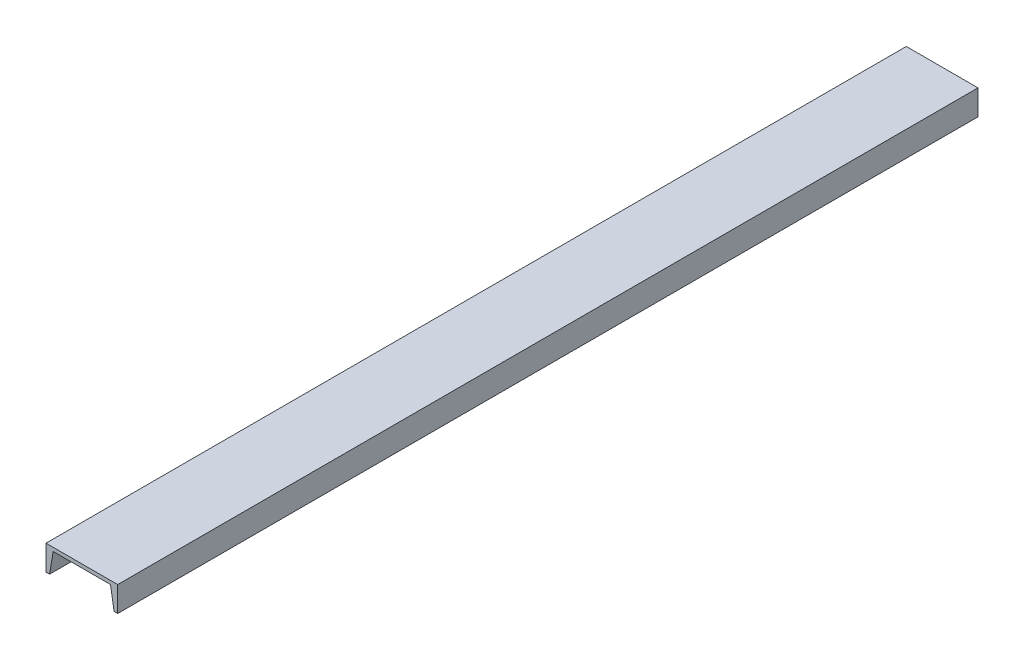
SolidWorks part; units mm, degrees
material "ASTM A36 Steel"
ref_plane "Front Plane" through (0, 0, 0) normal (0, 0, 1) x (1, 0, 0)
ref_plane "Top Plane" through (0, 0, 0) normal (0, 1, 0) x (1, 0, 0)
ref_plane "Right Plane" through (0, 0, 0) normal (1, 0, 0) x (0, 0, -1)
sketch "Sketch1" plane through (0, 0, 0) normal (0, 0, 1) x (1, 0, 0)
  line L0 (0, 0) -> (127, 0)
  line L1 (127, 0) -> (127, -44.45)
  line L2 (127, -44.45) -> (120.65, -44.45)
  line L3 (120.65, -44.45) -> (114.3, -6.35)
  line L4 (114.3, -6.35) -> (12.7, -6.35)
  line L5 (12.7, -6.35) -> (6.35, -44.45)
  line L6 (6.35, -44.45) -> (0, -44.45)
  line L7 (0, -44.45) -> (0, 0)
  point P3 (123.825, -44.45)
  dimension "D1" = 127
  dimension "D2" = 6.35
  dimension "D3" = 44.45
  dimension "D4" = 6.35
  dimension "D5" = 12.7
  dimension "D6" = 12.7
  dimension "D7" = 6.35
  dimension "D8" = 44.45
extrude "Boss-Extrude1" add sketch "Sketch1" along normal blind 1524
